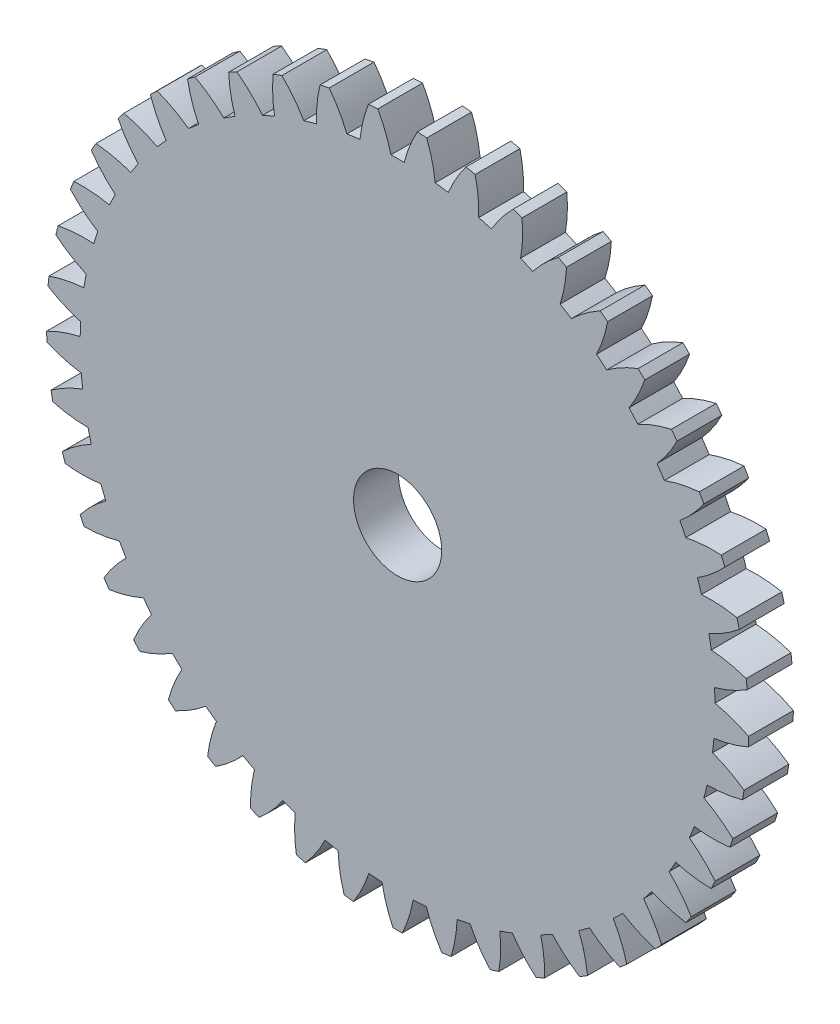
SolidWorks part; units mm, degrees
ref_plane "Front Plane" through (0, 0, 0) normal (0, 0, 1) x (1, 0, 0)
ref_plane "Top Plane" through (0, 0, 0) normal (0, 1, 0) x (1, 0, 0)
ref_plane "Right Plane" through (0, 0, 0) normal (1, 0, 0) x (0, 0, -1)
sketch "Model" plane through (0, 0, 0) normal (0, 0, 1) x (1, 0, 0)
  circle A0 centre (55.7791, 90.651) radius 15.95 construction
  arc A1 (32.4426, 93.4186) -> (32.3772, 92.7957) centre (55.7791, 90.651) ccw
  arc A2 (34.7806, 93.9041) -> (32.4426, 93.4186) centre (35.4255, 84.9273) ccw
  arc A3 (34.9343, 94.7759) -> (34.7806, 93.9041) centre (55.7791, 90.651) ccw
  arc A4 (32.9034, 96.0318) -> (34.9343, 94.7759) centre (38.6106, 102.9908) ccw
  arc A5 (33.0549, 96.6395) -> (32.9034, 96.0318) centre (55.7791, 90.651) ccw
  arc A6 (35.4377, 96.7949) -> (33.0549, 96.6395) centre (34.827, 87.8157) ccw
  arc A7 (35.7112, 97.6368) -> (35.4377, 96.7949) centre (55.7791, 90.651) ccw
  arc A8 (33.8749, 99.1631) -> (35.7112, 97.6368) centre (40.495, 105.2601) ccw
  arc A9 (34.1095, 99.7438) -> (33.8749, 99.1631) centre (55.7791, 90.651) ccw
  arc A10 (36.4907, 99.5661) -> (34.1095, 99.7438) centre (34.6363, 90.7592) ccw
  arc A11 (36.8788, 100.3617) -> (36.4907, 99.5661) centre (55.7791, 90.651) ccw
  arc A12 (35.2727, 102.1287) -> (36.8788, 100.3617) centre (42.677, 107.2451) ccw
  arc A13 (35.5859, 102.6711) -> (35.2727, 102.1287) centre (55.7791, 90.651) ccw
  arc A14 (37.9192, 102.1637) -> (35.5859, 102.6711) centre (34.8571, 93.7007) ccw
  arc A15 (38.4142, 102.8976) -> (37.9192, 102.1637) centre (55.7791, 90.651) ccw
  arc A16 (37.0697, 104.871) -> (38.4142, 102.8976) centre (45.1139, 108.907) ccw
  arc A17 (37.4553, 105.3645) -> (37.0697, 104.871) centre (55.7791, 90.651) ccw
  arc A18 (39.6953, 104.5373) -> (37.4553, 105.3645) centre (35.4852, 96.5828) ccw
  arc A19 (40.2876, 105.1951) -> (39.6953, 104.5373) centre (55.7791, 90.651) ccw
  arc A20 (39.2308, 107.3364) -> (40.2876, 105.1951) centre (47.7585, 110.2137) ccw
  arc A21 (39.6813, 107.7715) -> (39.2308, 107.3364) centre (55.7791, 90.651) ccw
  arc A22 (41.7844, 106.6406) -> (39.6813, 107.7715) centre (36.5082, 99.3494) ccw
  arc A23 (42.4625, 107.2096) -> (41.7844, 106.6406) centre (55.7791, 90.651) ccw
  arc A24 (41.714, 109.4771) -> (42.4625, 107.2096) centre (50.5591, 111.1395) ccw
  arc A25 (42.2207, 109.8452) -> (41.714, 109.4771) centre (55.7791, 90.651) ccw
  arc A26 (44.1459, 108.4327) -> (42.2207, 109.8452) centre (37.9063, 101.9467) ccw
  arc A27 (44.8966, 108.9018) -> (44.1459, 108.4327) centre (55.7791, 90.651) ccw
  arc A28 (44.471, 111.2514) -> (44.8966, 108.9018) centre (53.4614, 111.6666) ccw
  arc A29 (45.024, 111.5454) -> (44.471, 111.2514) centre (55.7791, 90.651) ccw
  arc A30 (46.7339, 109.8787) -> (45.024, 111.5454) centre (39.6523, 104.3242) ccw
  arc A31 (47.5425, 110.2387) -> (46.7339, 109.8787) centre (55.7791, 90.651) ccw
  arc A32 (47.4481, 112.6247) -> (47.5425, 110.2387) centre (56.4088, 111.7847) ccw
  arc A33 (48.0366, 112.8389) -> (47.4481, 112.6247) centre (55.7791, 90.651) ccw
  arc A34 (49.4979, 110.9504) -> (48.0366, 112.8389) centre (41.7122, 106.4356) ccw
  arc A35 (50.3488, 111.1944) -> (49.4979, 110.9504) centre (55.7791, 90.651) ccw
  arc A36 (50.5873, 113.5703) -> (50.3488, 111.1944) centre (59.3439, 111.4914) ccw
  arc A37 (51.1999, 113.7005) -> (50.5873, 113.5703) centre (55.7791, 90.651) ccw
  arc A38 (52.3842, 111.627) -> (51.1999, 113.7005) centre (44.0459, 108.2397) ccw
  arc A39 (53.2607, 111.7502) -> (52.3842, 111.627) centre (55.7791, 90.651) ccw
  arc A40 (53.8276, 114.0698) -> (53.2607, 111.7502) centre (62.2096, 110.7924) ccw
  arc A41 (54.4524, 114.1135) -> (53.8276, 114.0698) centre (55.7791, 90.651) ccw
  arc A42 (55.3365, 111.8954) -> (54.4524, 114.1135) centre (46.608, 109.7014) ccw
  arc A43 (56.2217, 111.8954) -> (55.3365, 111.8954) centre (55.7791, 90.651) ccw
  arc A44 (57.1058, 114.1135) -> (56.2217, 111.8954) centre (64.9502, 109.7014) ccw
  arc A45 (57.7306, 114.0698) -> (57.1058, 114.1135) centre (55.7791, 90.651) ccw
  arc A46 (58.2975, 111.7502) -> (57.7306, 114.0698) centre (49.3486, 110.7924) ccw
  arc A47 (59.174, 111.627) -> (58.2975, 111.7502) centre (55.7791, 90.651) ccw
  arc A48 (60.3583, 113.7005) -> (59.174, 111.627) centre (67.5123, 108.2397) ccw
  arc A49 (60.9709, 113.5703) -> (60.3583, 113.7005) centre (55.7791, 90.651) ccw
  arc A50 (61.2094, 111.1944) -> (60.9709, 113.5703) centre (52.2143, 111.4914) ccw
  arc A51 (62.0603, 110.9504) -> (61.2094, 111.1944) centre (55.7791, 90.651) ccw
  arc A52 (63.5216, 112.8389) -> (62.0603, 110.9504) centre (69.8459, 106.4356) ccw
  arc A53 (64.1101, 112.6247) -> (63.5216, 112.8389) centre (55.7791, 90.651) ccw
  arc A54 (64.0156, 110.2387) -> (64.1101, 112.6247) centre (55.1494, 111.7847) ccw
  arc A55 (64.8243, 109.8787) -> (64.0156, 110.2387) centre (55.7791, 90.651) ccw
  arc A56 (66.5342, 111.5454) -> (64.8243, 109.8787) centre (71.9058, 104.3242) ccw
  arc A57 (67.0872, 111.2514) -> (66.5342, 111.5454) centre (55.7791, 90.651) ccw
  arc A58 (66.6616, 108.9018) -> (67.0872, 111.2514) centre (58.0968, 111.6666) ccw
  arc A59 (67.4122, 108.4327) -> (66.6616, 108.9018) centre (55.7791, 90.651) ccw
  arc A60 (69.3375, 109.8452) -> (67.4122, 108.4327) centre (73.6518, 101.9467) ccw
  arc A61 (69.8442, 109.4771) -> (69.3375, 109.8452) centre (55.7791, 90.651) ccw
  arc A62 (69.0957, 107.2096) -> (69.8442, 109.4771) centre (60.999, 111.1395) ccw
  arc A63 (69.7738, 106.6406) -> (69.0957, 107.2096) centre (55.7791, 90.651) ccw
  arc A64 (71.8768, 107.7715) -> (69.7738, 106.6406) centre (75.05, 99.3494) ccw
  arc A65 (72.3274, 107.3364) -> (71.8768, 107.7715) centre (55.7791, 90.651) ccw
  arc A66 (71.2706, 105.1951) -> (72.3274, 107.3364) centre (63.7997, 110.2137) ccw
  arc A67 (71.8629, 104.5373) -> (71.2706, 105.1951) centre (55.7791, 90.651) ccw
  arc A68 (74.1029, 105.3645) -> (71.8629, 104.5373) centre (76.073, 96.5828) ccw
  arc A69 (74.4885, 104.871) -> (74.1029, 105.3645) centre (55.7791, 90.651) ccw
  arc A70 (73.144, 102.8976) -> (74.4885, 104.871) centre (66.4442, 108.907) ccw
  arc A71 (73.639, 102.1637) -> (73.144, 102.8976) centre (55.7791, 90.651) ccw
  arc A72 (75.9723, 102.6711) -> (73.639, 102.1637) centre (76.7011, 93.7007) ccw
  arc A73 (76.2855, 102.1287) -> (75.9723, 102.6711) centre (55.7791, 90.651) ccw
  arc A74 (74.6794, 100.3617) -> (76.2855, 102.1287) centre (68.8812, 107.2451) ccw
  arc A75 (75.0674, 99.5661) -> (74.6794, 100.3617) centre (55.7791, 90.651) ccw
  arc A76 (77.4487, 99.7438) -> (75.0674, 99.5661) centre (76.9219, 90.7592) ccw
  arc A77 (77.6833, 99.1631) -> (77.4487, 99.7438) centre (55.7791, 90.651) ccw
  arc A78 (75.8469, 97.6368) -> (77.6833, 99.1631) centre (71.0632, 105.2601) ccw
  arc A79 (76.1205, 96.7949) -> (75.8469, 97.6368) centre (55.7791, 90.651) ccw
  arc A80 (78.5033, 96.6395) -> (76.1205, 96.7949) centre (76.7312, 87.8157) ccw
  arc A81 (78.6548, 96.0318) -> (78.5033, 96.6395) centre (55.7791, 90.651) ccw
  arc A82 (76.6239, 94.7759) -> (78.6548, 96.0318) centre (72.9476, 102.9908) ccw
  arc A83 (76.7776, 93.9041) -> (76.6239, 94.7759) centre (55.7791, 90.651) ccw
  arc A84 (79.1155, 93.4186) -> (76.7776, 93.9041) centre (76.1327, 84.9273) ccw
  arc A85 (79.181, 92.7957) -> (79.1155, 93.4186) centre (55.7791, 90.651) ccw
  arc A86 (76.9951, 91.8347) -> (79.181, 92.7957) centre (74.4979, 100.4813) ccw
  arc A87 (77.026, 90.9501) -> (76.9951, 91.8347) centre (55.7791, 90.651) ccw
  arc A88 (79.2736, 90.1439) -> (77.026, 90.9501) centre (75.138, 82.1503) ccw
  arc A89 (79.2518, 89.5179) -> (79.2736, 90.1439) centre (55.7791, 90.651) ccw
  arc A90 (76.9534, 88.8705) -> (79.2518, 89.5179) centre (75.6839, 97.7805) ccw
  arc A91 (76.8608, 87.9902) -> (76.9534, 88.8705) centre (55.7791, 90.651) ccw
  arc A92 (78.9744, 86.879) -> (76.8608, 87.9902) centre (73.7666, 79.5388) ccw
  arc A93 (78.8656, 86.2622) -> (78.9744, 86.879) centre (55.7791, 90.651) ccw
  arc A94 (76.4995, 85.9409) -> (78.8656, 86.2622) centre (76.4824, 94.9409) ccw
  arc A95 (76.2854, 85.082) -> (76.4995, 85.9409) centre (55.7791, 90.651) ccw
  arc A96 (78.2237, 83.6875) -> (76.2854, 85.082) centre (72.045, 77.1436) ccw
  arc A97 (78.0302, 83.0919) -> (78.2237, 83.6875) centre (55.7791, 90.651) ccw
  arc A98 (75.6423, 83.103) -> (78.0302, 83.0919) centre (76.8779, 92.0178) ccw
  arc A99 (75.3107, 82.2823) -> (75.6423, 83.103) centre (55.7791, 90.651) ccw
  arc A100 (77.0362, 80.6316) -> (75.3107, 82.2823) centre (70.0068, 75.0112) ccw
  arc A101 (76.7616, 80.0687) -> (77.0362, 80.6316) centre (55.7791, 90.651) ccw
  arc A102 (74.3986, 80.4121) -> (76.7616, 80.0687) centre (76.8628, 89.0681) ccw
  arc A103 (73.956, 79.6455) -> (74.3986, 80.4121) centre (55.7791, 90.651) ccw
  arc A104 (75.4349, 77.7707) -> (73.956, 79.6455) centre (67.6917, 73.1833) ccw
  arc A105 (75.0846, 77.2515) -> (75.4349, 77.7707) centre (55.7791, 90.651) ccw
  arc A106 (72.7924, 77.9204) -> (75.0846, 77.2515) centre (76.4374, 86.1492) ccw
  arc A107 (72.2474, 77.2228) -> (72.7924, 77.9204) centre (55.7791, 90.651) ccw
  arc A108 (73.451, 75.1605) -> (72.2474, 77.2228) centre (65.1448, 71.6954) ccw
  arc A109 (73.0319, 74.6951) -> (73.451, 75.1605) centre (55.7791, 90.651) ccw
  arc A110 (70.8551, 75.6765) -> (73.0319, 74.6951) centre (75.6098, 83.318) ccw
  arc A111 (70.2183, 75.0616) -> (70.8551, 75.6765) centre (55.7791, 90.651) ccw
  arc A112 (71.1231, 72.8518) -> (70.2183, 75.0616) centre (62.4155, 70.5764) ccw
  arc A113 (70.6434, 72.4492) -> (71.1231, 72.8518) centre (55.7791, 90.651) ccw
  arc A114 (68.6243, 73.724) -> (70.6434, 72.4492) centre (74.3963, 80.6294) ccw
  arc A115 (67.9082, 73.2037) -> (68.6243, 73.724) centre (55.7791, 90.651) ccw
  arc A116 (68.4967, 70.8895) -> (67.9082, 73.2037) centre (59.5571, 69.8482) ccw
  arc A117 (67.9655, 70.5577) -> (68.4967, 70.8895) centre (55.7791, 90.651) ccw
  arc A118 (66.1435, 72.1011) -> (67.9655, 70.5577) centre (72.8203, 78.136) ccw
  arc A119 (65.3619, 71.6855) -> (66.1435, 72.1011) centre (55.7791, 90.651) ccw
  arc A120 (65.6226, 69.3119) -> (65.3619, 71.6855) centre (56.6252, 69.5248) ccw
  arc A121 (65.0505, 69.0572) -> (65.6226, 69.3119) centre (55.7791, 90.651) ccw
  arc A122 (63.461, 70.8391) -> (65.0505, 69.0572) centre (70.9128, 75.8861) ccw
  arc A123 (62.6292, 70.5364) -> (63.461, 70.8391) centre (55.7791, 90.651) ccw
  arc A124 (62.557, 68.1496) -> (62.6292, 70.5364) centre (53.6767, 69.6127) ccw
  arc A125 (61.955, 67.977) -> (62.557, 68.1496) centre (55.7791, 90.651) ccw
  arc A126 (60.629, 69.9628) -> (61.955, 67.977) centre (68.7106, 73.9236) ccw
  arc A127 (59.7631, 69.7788) -> (60.629, 69.9628) centre (55.7791, 90.651) ccw
  arc A128 (59.3595, 67.4253) -> (59.7631, 69.7788) centre (50.7692, 70.11) ccw
  arc A129 (58.7393, 67.3381) -> (59.3595, 67.4253) centre (55.7791, 90.651) ccw
  arc A130 (57.7025, 69.4892) -> (58.7393, 67.3381) centre (66.2567, 72.2866) ccw
  arc A131 (56.8195, 69.4274) -> (57.7025, 69.4892) centre (55.7791, 90.651) ccw
  arc A132 (56.0922, 67.1531) -> (56.8195, 69.4274) centre (47.9592, 71.0071) ccw
  arc A133 (55.4659, 67.1531) -> (56.0922, 67.1531) centre (55.7791, 90.651) ccw
  arc A134 (54.7387, 69.4274) -> (55.4659, 67.1531) centre (63.599, 71.0071) ccw
  arc A135 (53.8556, 69.4892) -> (54.7387, 69.4274) centre (55.7791, 90.651) ccw
  arc A136 (52.8189, 67.3381) -> (53.8556, 69.4892) centre (45.3014, 72.2866) ccw
  arc A137 (52.1987, 67.4253) -> (52.8189, 67.3381) centre (55.7791, 90.651) ccw
  arc A138 (51.7951, 69.7788) -> (52.1987, 67.4253) centre (60.789, 70.11) ccw
  arc A139 (50.9292, 69.9628) -> (51.7951, 69.7788) centre (55.7791, 90.651) ccw
  arc A140 (49.6032, 67.977) -> (50.9292, 69.9628) centre (42.8476, 73.9236) ccw
  arc A141 (49.0012, 68.1496) -> (49.6032, 67.977) centre (55.7791, 90.651) ccw
  arc A142 (48.929, 70.5364) -> (49.0012, 68.1496) centre (57.8815, 69.6127) ccw
  arc A143 (48.0972, 70.8391) -> (48.929, 70.5364) centre (55.7791, 90.651) ccw
  arc A144 (46.5077, 69.0572) -> (48.0972, 70.8391) centre (40.6454, 75.8861) ccw
  arc A145 (45.9355, 69.3119) -> (46.5077, 69.0572) centre (55.7791, 90.651) ccw
  arc A146 (46.1962, 71.6855) -> (45.9355, 69.3119) centre (54.933, 69.5248) ccw
  arc A147 (45.4147, 72.1011) -> (46.1962, 71.6855) centre (55.7791, 90.651) ccw
  arc A148 (43.5927, 70.5577) -> (45.4147, 72.1011) centre (38.7378, 78.136) ccw
  arc A149 (43.0615, 70.8895) -> (43.5927, 70.5577) centre (55.7791, 90.651) ccw
  arc A150 (43.65, 73.2037) -> (43.0615, 70.8895) centre (52.0011, 69.8482) ccw
  arc A151 (42.9339, 73.724) -> (43.65, 73.2037) centre (55.7791, 90.651) ccw
  arc A152 (40.9148, 72.4492) -> (42.9339, 73.724) centre (37.1619, 80.6294) ccw
  arc A153 (40.435, 72.8518) -> (40.9148, 72.4492) centre (55.7791, 90.651) ccw
  arc A154 (41.3399, 75.0616) -> (40.435, 72.8518) centre (49.1426, 70.5764) ccw
  arc A155 (40.7031, 75.6765) -> (41.3399, 75.0616) centre (55.7791, 90.651) ccw
  arc A156 (38.5263, 74.6951) -> (40.7031, 75.6765) centre (35.9484, 83.318) ccw
  arc A157 (38.1072, 75.1605) -> (38.5263, 74.6951) centre (55.7791, 90.651) ccw
  arc A158 (39.3108, 77.2228) -> (38.1072, 75.1605) centre (46.4134, 71.6954) ccw
  arc A159 (38.7658, 77.9204) -> (39.3108, 77.2228) centre (55.7791, 90.651) ccw
  arc A160 (36.4736, 77.2515) -> (38.7658, 77.9204) centre (35.1208, 86.1492) ccw
  arc A161 (36.1233, 77.7707) -> (36.4736, 77.2515) centre (55.7791, 90.651) ccw
  arc A162 (37.6022, 79.6455) -> (36.1233, 77.7707) centre (43.8664, 73.1833) ccw
  arc A163 (37.1596, 80.4121) -> (37.6022, 79.6455) centre (55.7791, 90.651) ccw
  arc A164 (34.7966, 80.0687) -> (37.1596, 80.4121) centre (34.6953, 89.0681) ccw
  arc A165 (34.522, 80.6316) -> (34.7966, 80.0687) centre (55.7791, 90.651) ccw
  arc A166 (36.2474, 82.2823) -> (34.522, 80.6316) centre (41.5513, 75.0112) ccw
  arc A167 (35.9158, 83.103) -> (36.2474, 82.2823) centre (55.7791, 90.651) ccw
  arc A168 (33.528, 83.0919) -> (35.9158, 83.103) centre (34.6802, 92.0178) ccw
  arc A169 (33.3345, 83.6875) -> (33.528, 83.0919) centre (55.7791, 90.651) ccw
  arc A170 (35.2728, 85.082) -> (33.3345, 83.6875) centre (39.5132, 77.1436) ccw
  arc A171 (35.0587, 85.9409) -> (35.2728, 85.082) centre (55.7791, 90.651) ccw
  arc A172 (32.6925, 86.2622) -> (35.0587, 85.9409) centre (35.0758, 94.9409) ccw
  arc A173 (32.5838, 86.879) -> (32.6925, 86.2622) centre (55.7791, 90.651) ccw
  arc A174 (34.6973, 87.9902) -> (32.5838, 86.879) centre (37.7916, 79.5388) ccw
  arc A175 (34.6048, 88.8705) -> (34.6973, 87.9902) centre (55.7791, 90.651) ccw
  arc A176 (32.3064, 89.5179) -> (34.6048, 88.8705) centre (35.8743, 97.7805) ccw
  arc A177 (32.2846, 90.1439) -> (32.3064, 89.5179) centre (55.7791, 90.651) ccw
  arc A178 (34.5322, 90.9501) -> (32.2846, 90.1439) centre (36.4201, 82.1503) ccw
  arc A179 (34.5631, 91.8347) -> (34.5322, 90.9501) centre (55.7791, 90.651) ccw
  arc A180 (32.3772, 92.7957) -> (34.5631, 91.8347) centre (37.0603, 100.4813) ccw
extrude "Boss-Extrude1" add sketch "Model" along normal blind 3
sketch "Sketch2" plane through (0, 0, 3) normal (0, 0, 1) x (1, 0, 0)
  circle A0 centre (55.7791, 90.651) radius 21.249 construction
  circle A1 centre (55.7791, 90.651) radius 2.95
  dimension "D1" = 5.9
extrude "Cut-Extrude1" cut sketch "Sketch2" against normal blind 3
sketch "Sketch3" plane through (0, 0, 3) normal (0, 0, 1) x (1, 0, 0)
  line L0 (55.7791, 90.651) -> (61.7791, 90.651) construction
  circle A0 centre (61.7791, 90.651) radius 1.75
  dimension "D1" = 3.5
  dimension "D2" = 6
extrude "Cut-Extrude2" [suppressed] cut sketch "Sketch3" against normal blind 3
pattern_circular "CirPattern1" [suppressed] count 4 over 360
sketch "Sketch6" plane through (0, 0, 0) normal (0, 0, 1) x (1, 0, 0)
  circle A0 centre (55.7791, 90.651) radius 22.5 construction
  dimension "D1" = 45
